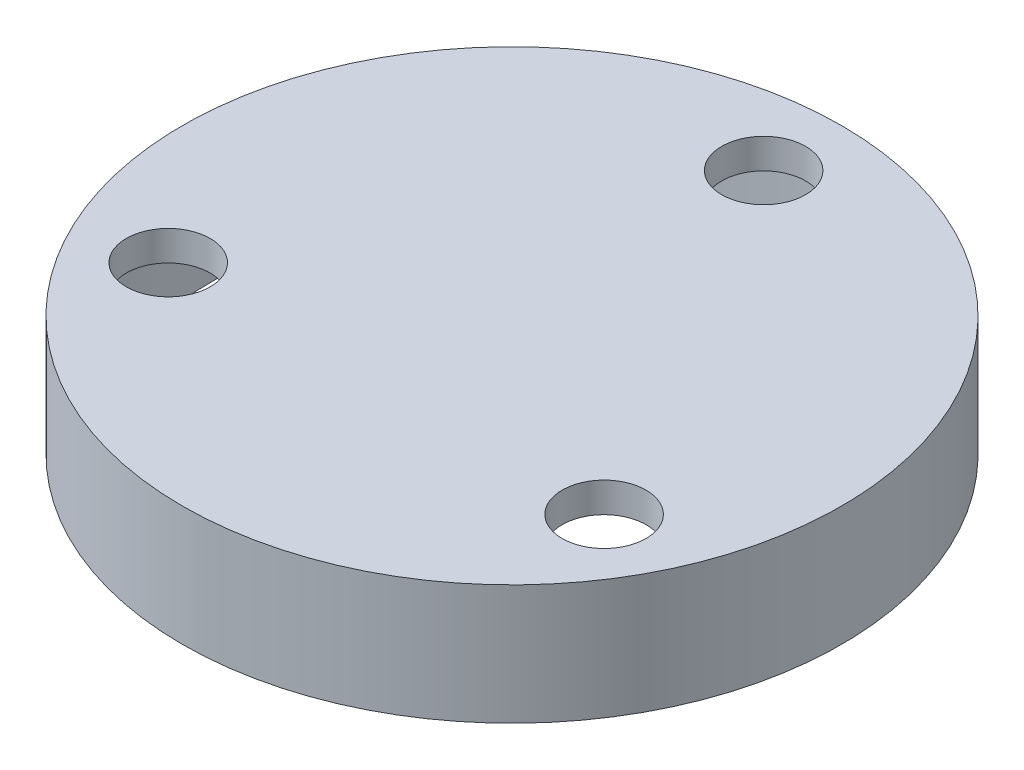
SolidWorks part; units mm, degrees
ref_plane "Front Plane" through (0, 0, 0) normal (0, 0, 1) x (1, 0, 0)
ref_plane "Top Plane" through (0, 0, 0) normal (0, 1, 0) x (1, 0, 0)
ref_plane "Right Plane" through (0, 0, 0) normal (1, 0, 0) x (0, 0, -1)
sketch "Sketch1" plane through (0, 0, 0) normal (0, 1, 0) x (1, 0, 0)
  circle A0 centre (0, 0) radius 55
  circle A1 centre (0, 0) radius 42 construction
  circle A2 centre (0, 42) radius 7
  circle A3 centre (36.3731, -21) radius 7
  circle A4 centre (-36.3731, -21) radius 7
  point P13 (0, 0)
  dimension "D1" = 14
  dimension "D2" = 110
  dimension "D3" = 84
  dimension "D4" = 3
extrude "Boss-Extrude1" add sketch "Sketch1" along normal blind 20
sketch "Sketch2" plane through (0, 0, 0) normal (0, -1, 0) x (1, 0, 0)
  circle A0 centre (0, 0) radius 50
  circle A1 centre (0, 0) radius 55
  circle A2 centre (0, 0) radius 55
  circle M4 centre (0, -42) radius 7
  circle M5 centre (36.3731, 21) radius 7
  circle M6 centre (-36.3731, 21) radius 7
  dimension "D1" = 0
  dimension "D2" = 5
extrude "Cut-Extrude1" cut sketch "Sketch2" against normal offset from surface (15 mm away) 5 contours A0 M5 M6 M4 up to face at (36.3731, 20, 28)
